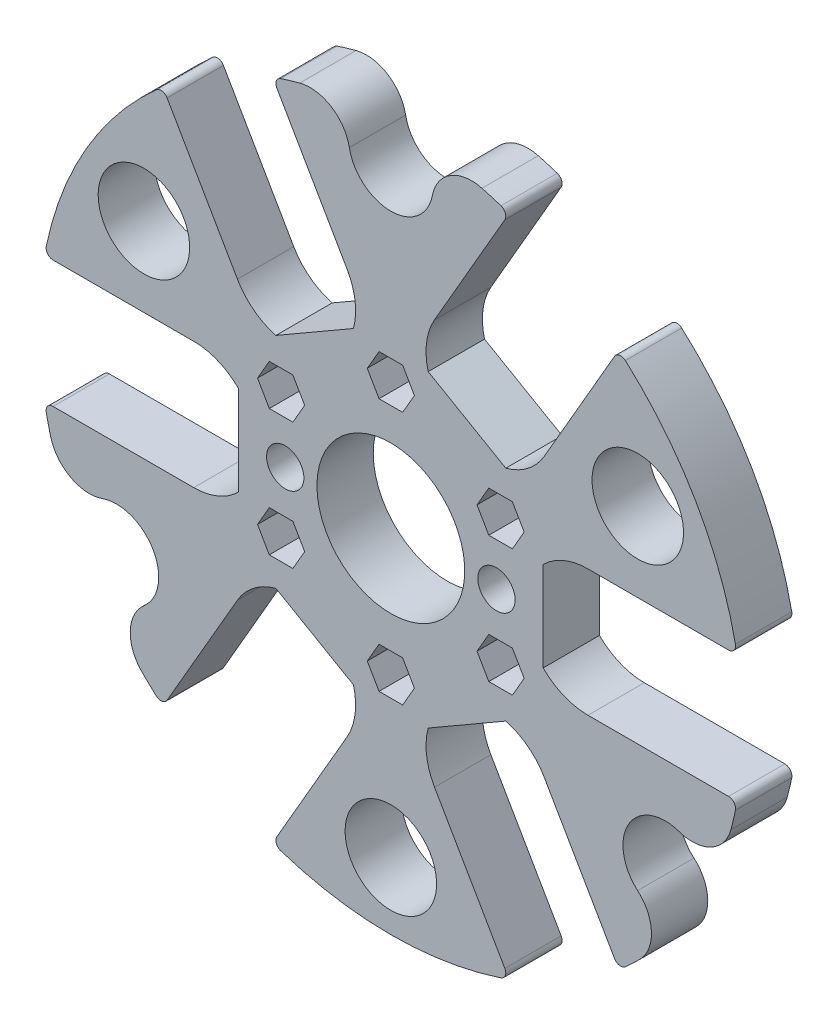
SolidWorks part; units mm, degrees
ref_plane "前视基准面" through (0, 0, 0) normal (0, 0, 1) x (1, 0, 0)
ref_plane "上视基准面" through (0, 0, 0) normal (0, 1, 0) x (1, 0, 0)
ref_plane "右视基准面" through (0, 0, 0) normal (1, 0, 0) x (0, 0, -1)
ref_plane "基准面4" through (0, 0, 0) normal (0, -1, 0) x (1, 0, 0)
sketch "草图1" plane through (0, 0, 0) normal (0, -1, 0) x (1, 0, 0)
  line L0 (500, 8) -> (450, 8)
  line L1 (450, 8) -> (450, 0)
  line L2 (450, 0) -> (500, 0)
  line L3 (500, 0) -> (500, 8)
  line L4 (450, 8) -> (450, 0) construction
revolve "旋转1" add sketch "草图1" angle 360 about L4
sketch "草图2" plane through (0, 0, 0) normal (0, 0, -1) x (-1, 0, 0)
  line L0 (-499.1833, -9) -> (-478, -9)
  line L1 (-471.636, -6.364) -> (-471.636, 6.364)
  line L2 (-478, 9) -> (-499.1833, 9)
  arc A0 (-499.1833, 9) -> (-499.1833, -9) centre (-450, 0) ccw
  arc A1 (-478, -9) -> (-471.636, -6.364) centre (-478, 0) ccw
  arc A2 (-471.636, 6.364) -> (-478, 9) centre (-478, 0) ccw
extrude "切除-拉伸1" cut sketch "草图2" against normal through all
sketch "草图3" plane through (0, 0, 0) normal (0, 0, -1) x (-1, 0, 0)
  line L0 (-482.3859, 38.094) -> (-471.7942, 19.7487)
  line L1 (-466.3294, 15.5554) -> (-455.3067, 21.9193)
  line L2 (-456.2058, 28.7487) -> (-466.7974, 47.094)
  arc A0 (-466.7974, 47.094) -> (-482.3859, 38.094) centre (-450, 0) ccw
  arc A1 (-471.7942, 19.7487) -> (-466.3294, 15.5554) centre (-464, 24.2487) ccw
  arc A2 (-455.3067, 21.9193) -> (-456.2058, 28.7487) centre (-464, 24.2487) ccw
extrude "切除-拉伸2" cut sketch "草图3" against normal through all
sketch "草图4" plane through (0, 0, 0) normal (0, 0, -1) x (-1, 0, 0)
  line L0 (-433.2026, 47.094) -> (-443.7942, 28.7487)
  line L1 (-444.6933, 21.9193) -> (-433.6706, 15.5554)
  line L2 (-428.2058, 19.7487) -> (-417.6141, 38.094)
  arc A0 (-417.6141, 38.094) -> (-433.2026, 47.094) centre (-450, 0) ccw
  arc A1 (-443.7942, 28.7487) -> (-444.6933, 21.9193) centre (-436, 24.2487) ccw
  arc A2 (-433.6706, 15.5554) -> (-428.2058, 19.7487) centre (-436, 24.2487) ccw
extrude "切除-拉伸3" cut sketch "草图4" against normal through all
sketch "草图5" plane through (0, 0, 0) normal (0, 0, -1) x (-1, 0, 0)
  line L0 (-400.8167, 9) -> (-422, 9)
  line L1 (-428.364, 6.364) -> (-428.364, -6.364)
  line L2 (-422, -9) -> (-400.8167, -9)
  arc A0 (-400.8167, -9) -> (-400.8167, 9) centre (-450, 0) ccw
  arc A1 (-422, 9) -> (-428.364, 6.364) centre (-422, 0) ccw
  arc A2 (-428.364, -6.364) -> (-422, -9) centre (-422, 0) ccw
extrude "切除-拉伸4" cut sketch "草图5" against normal through all
sketch "草图6" plane through (0, 0, 0) normal (0, 0, -1) x (-1, 0, 0)
  line L0 (-417.6141, -38.094) -> (-428.2058, -19.7487)
  line L1 (-433.6706, -15.5554) -> (-444.6933, -21.9193)
  line L2 (-443.7942, -28.7487) -> (-433.2026, -47.094)
  arc A0 (-433.2026, -47.094) -> (-417.6141, -38.094) centre (-450, 0) ccw
  arc A1 (-428.2058, -19.7487) -> (-433.6706, -15.5554) centre (-436, -24.2487) ccw
  arc A2 (-444.6933, -21.9193) -> (-443.7942, -28.7487) centre (-436, -24.2487) ccw
extrude "切除-拉伸5" cut sketch "草图6" against normal through all
sketch "草图7" plane through (0, 0, 0) normal (0, 0, -1) x (-1, 0, 0)
  line L0 (-466.7974, -47.094) -> (-456.2058, -28.7487)
  line L1 (-455.3067, -21.9193) -> (-466.3294, -15.5554)
  line L2 (-471.7942, -19.7487) -> (-482.3859, -38.094)
  arc A0 (-482.3859, -38.094) -> (-466.7974, -47.094) centre (-450, 0) ccw
  arc A1 (-456.2058, -28.7487) -> (-455.3067, -21.9193) centre (-464, -24.2487) ccw
  arc A2 (-466.3294, -15.5554) -> (-471.7942, -19.7487) centre (-464, -24.2487) ccw
extrude "切除-拉伸6" cut sketch "草图7" against normal through all
sketch "草图8" plane through (0, 0, 8) normal (0, 0, 1) x (1, 0, 0)
  line L0 (451.675, 15.0988) -> (453.35, 18)
  line L1 (453.35, 18) -> (451.675, 20.9012)
  line L2 (451.675, 20.9012) -> (448.325, 20.9012)
  line L3 (448.325, 20.9012) -> (446.65, 18)
  line L4 (446.65, 18) -> (448.325, 15.0988)
  line L5 (448.325, 15.0988) -> (451.675, 15.0988)
extrude "切除-拉伸7" cut sketch "草图8" against normal blind 5
sketch "草图9" plane through (0, 0, 8) normal (0, 0, 1) x (1, 0, 0)
  line L0 (436.0865, 11.9012) -> (432.7365, 11.9012)
  line L1 (432.7365, 11.9012) -> (431.0615, 9)
  line L2 (431.0615, 9) -> (432.7365, 6.0988)
  line L3 (432.7365, 6.0988) -> (436.0865, 6.0988)
  line L4 (436.0865, 6.0988) -> (437.7615, 9)
  line L5 (437.7615, 9) -> (436.0865, 11.9012)
extrude "切除-拉伸8" cut sketch "草图9" against normal blind 5
sketch "草图10" plane through (0, 0, 8) normal (0, 0, 1) x (1, 0, 0)
  line L0 (432.7365, -6.0988) -> (431.0615, -9)
  line L1 (431.0615, -9) -> (432.7365, -11.9012)
  line L2 (432.7365, -11.9012) -> (436.0865, -11.9012)
  line L3 (436.0865, -11.9012) -> (437.7615, -9)
  line L4 (437.7615, -9) -> (436.0865, -6.0988)
  line L5 (436.0865, -6.0988) -> (432.7365, -6.0988)
extrude "切除-拉伸9" cut sketch "草图10" against normal blind 5
sketch "草图11" plane through (0, 0, 8) normal (0, 0, 1) x (1, 0, 0)
  line L0 (446.65, -18) -> (448.325, -20.9012)
  line L1 (448.325, -20.9012) -> (451.675, -20.9012)
  line L2 (451.675, -20.9012) -> (453.35, -18)
  line L3 (453.35, -18) -> (451.675, -15.0988)
  line L4 (451.675, -15.0988) -> (448.325, -15.0988)
  line L5 (448.325, -15.0988) -> (446.65, -18)
extrude "切除-拉伸10" cut sketch "草图11" against normal blind 5
sketch "草图12" plane through (0, 0, 8) normal (0, 0, 1) x (1, 0, 0)
  line L0 (463.9135, -11.9012) -> (467.2635, -11.9012)
  line L1 (467.2635, -11.9012) -> (468.9385, -9)
  line L2 (468.9385, -9) -> (467.2635, -6.0988)
  line L3 (467.2635, -6.0988) -> (463.9135, -6.0988)
  line L4 (463.9135, -6.0988) -> (462.2385, -9)
  line L5 (462.2385, -9) -> (463.9135, -11.9012)
extrude "切除-拉伸11" cut sketch "草图12" against normal blind 5
sketch "草图13" plane through (0, 0, 8) normal (0, 0, 1) x (1, 0, 0)
  line L0 (467.2635, 6.0988) -> (468.9385, 9)
  line L1 (468.9385, 9) -> (467.2635, 11.9012)
  line L2 (467.2635, 11.9012) -> (463.9135, 11.9012)
  line L3 (463.9135, 11.9012) -> (462.2385, 9)
  line L4 (462.2385, 9) -> (463.9135, 6.0988)
  line L5 (463.9135, 6.0988) -> (467.2635, 6.0988)
extrude "切除-拉伸12" cut sketch "草图13" against normal blind 5
hole_wizard "Ø3.6 (3.6) 直径孔1" positions "草图15" profile "草图14" hole size "Ø3.6" standard "ANSI Metric"
sketch "草图15" plane through (0, 0, 0) normal (0, 0, -1) x (-1, 0, 0)
  point P0 (-450, 18)
  point P1 (-434.4115, 9)
  point P2 (-434.4115, -9)
  point P3 (-450, -18)
  point P4 (-465.5885, -9)
  point P5 (-465.5885, 9)
sketch "草图14" plane through (450, 18, 0) normal (1, 0, 0) x (0, 1, 0)
  line L0 (0, 0) -> (0, 8)
  line L1 (0, 8) -> (1.8, 8)
  line L2 (1.8, 8) -> (1.8, 0)
  line L5 (1.8, 0) -> (0, 0)
  line L11 (0, -6.35) -> (0, 107.95) construction
  dimension "通孔孔直径" = 3.6
  dimension "通孔孔深度" = 8
hole_wizard "Ø5.3 (5.3) 直径孔1" positions "草图17" profile "草图16" hole size "Ø5.3" standard "ANSI Metric"
sketch "草图17" plane through (0, 0, 0) normal (0, 0, -1) x (-1, 0, 0)
  point P0 (-465, 0)
  point P1 (-435, 0)
sketch "草图16" plane through (465, 0, 0) normal (1, 0, 0) x (0, 1, 0)
  line L0 (0, 0) -> (0, 8)
  line L1 (0, 8) -> (2.65, 8)
  line L2 (2.65, 8) -> (2.65, 0)
  line L5 (2.65, 0) -> (0, 0)
  line L11 (0, -6.35) -> (0, 107.95) construction
  dimension "通孔孔直径" = 5.3
  dimension "通孔孔深度" = 8
hole_wizard "Ø21.0 (21) 直径孔1" positions "草图19" profile "草图18" hole size "Ø21.0" standard "ANSI Metric"
sketch "草图19" plane through (0, 0, 0) normal (0, 0, -1) x (-1, 0, 0)
  point P0 (-450, 0)
sketch "草图18" plane through (450, 0, 0) normal (1, 0, 0) x (0, 1, 0)
  line L0 (0, 0) -> (0, 8)
  line L1 (0, 8) -> (10.5, 8)
  line L2 (10.5, 8) -> (10.5, 0)
  line L5 (10.5, 0) -> (0, 0)
  line L11 (0, -6.35) -> (0, 107.95) construction
  dimension "通孔孔直径" = 21
  dimension "通孔孔深度" = 8
hole_wizard "Ø13.0 (13) 直径孔1" positions "草图21" profile "草图20" hole size "Ø13.0" standard "ANSI Metric"
sketch "草图21" plane through (0, 0, 0) normal (0, 0, -1) x (-1, 0, 0)
  point P0 (-450, -40.5)
  point P1 (-485.074, 20.25)
  point P2 (-414.926, 20.25)
sketch "草图20" plane through (450, -40.5, 0) normal (1, 0, 0) x (0, 1, 0)
  line L0 (0, 0) -> (0, 8)
  line L1 (0, 8) -> (6.5, 8)
  line L2 (6.5, 8) -> (6.5, 0)
  line L5 (6.5, 0) -> (0, 0)
  line L11 (0, -6.35) -> (0, 107.95) construction
  dimension "通孔孔直径" = 13
  dimension "通孔孔深度" = 8
hole_wizard "Ø12.0 (12) 直径孔1" positions "草图23" profile "草图22" hole size "Ø12.0" standard "ANSI Metric"
sketch "草图23" plane through (0, 0, 8) normal (0, 0, 1) x (1, 0, 0)
  point P0 (488.9711, -22.5)
  point P1 (450, 45)
  point P2 (411.0289, -22.5)
sketch "草图22" plane through (488.9711, -22.5, 8) normal (1, 0, 0) x (0, -1, 0)
  line L0 (0, 0) -> (0, 8)
  line L1 (0, 8) -> (6, 8)
  line L2 (6, 8) -> (6, 0)
  line L5 (6, 0) -> (0, 0)
  line L11 (0, -6.35) -> (0, 107.95) construction
  dimension "通孔孔直径" = 12
  dimension "通孔孔深度" = 8
fillet "圆角1" radius 1 12 edges at (400.8167, 9, 4) (466.7974, -47.094, 4) (417.6141, -38.094, 4) (499.1833, -9, 4) (417.6141, 38.094, 4) (499.1833, 9, 4) (400.8167, -9, 4) (482.3859, 38.094, 4) (433.2026, -47.094, 4) (466.7974, 47.094, 4) (482.3859, -38.094, 4) (433.2026, 47.094, 4)
fillet "圆角2" radius 5.6782 6 edges at (405.0576, -21.9131, 4) (408.5515, -27.9647, 4) (491.4485, -27.9647, 4) (494.9424, -21.9131, 4) (453.4939, 49.8778, 4) (446.5061, 49.8778, 4)
